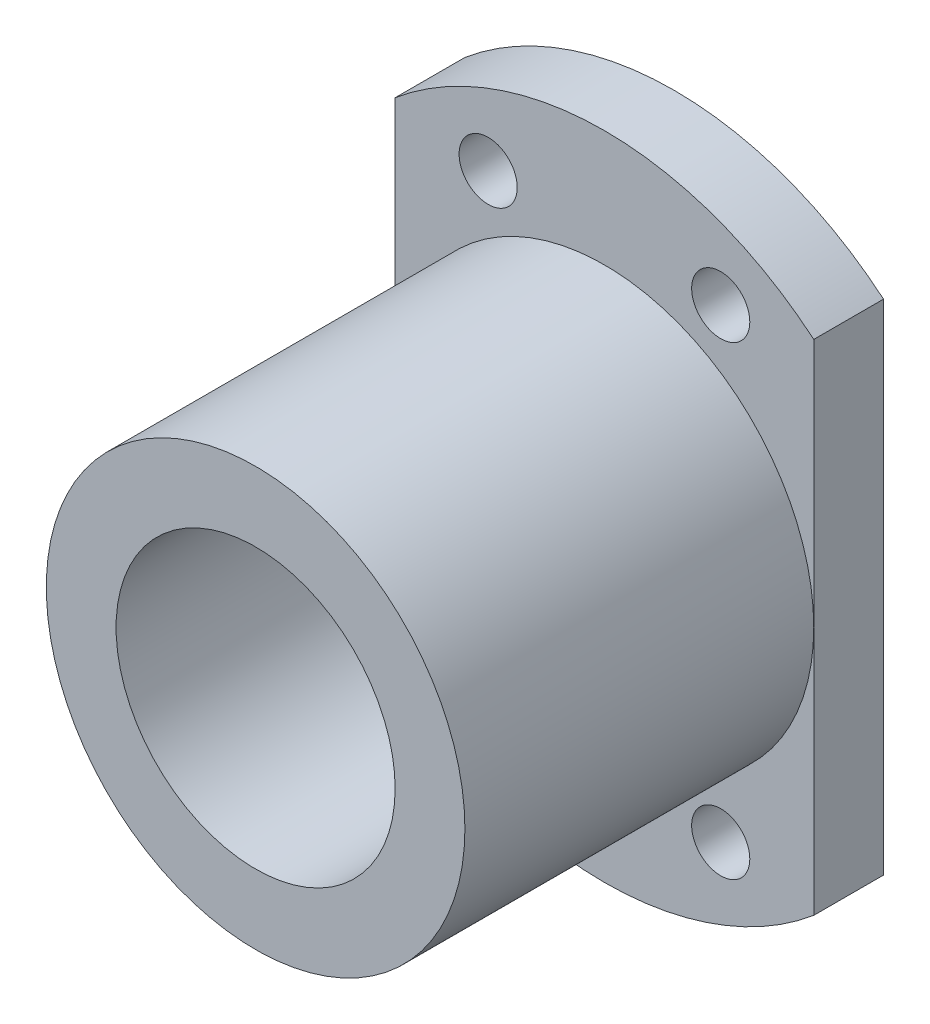
SolidWorks part; units mm, degrees
ref_plane "Front Plane" through (0, 0, 0) normal (0, 0, 1) x (1, 0, 0)
ref_plane "Top Plane" through (0, 0, 0) normal (0, 1, 0) x (1, 0, 0)
ref_plane "Right Plane" through (0, 0, 0) normal (1, 0, 0) x (0, 0, -1)
sketch "Sketch1" plane through (0, 0, 0) normal (0, 0, 1) x (1, 0, 0)
  line L0 (-9, 10.7238) -> (-9, -10.7238)
  line L1 (9, 10.7238) -> (9, -10.7238)
  line L2 (-9, 0) -> (9, 0) construction
  line L3 (-5, 10) -> (5, -10) construction
  line L4 (-5, -10) -> (5, 10) construction
  arc A0 (9, 10.7238) -> (-9, 10.7238) centre (0, 0) ccw
  arc A1 (-9, -10.7238) -> (9, -10.7238) centre (0, 0) ccw
  circle A2 centre (0, 0) radius 6
  circle A3 centre (-5, 10) radius 1.25
  circle A4 centre (5, 10) radius 1.25
  circle A5 centre (-5, -10) radius 1.25
  circle A6 centre (5, -10) radius 1.25
  point P7 (0, 0)
  point P18 (0, 0)
  dimension "D2" = 14
  dimension "D3" = 12
  dimension "D6" = 2.5
  dimension "D1" = 18
  dimension "D4" = 20
  dimension "D5" = 10
extrude "Boss-Extrude1" add sketch "Sketch1" along normal blind 3
sketch "Sketch2" plane through (0, 0, 3) normal (0, 0, 1) x (1, 0, 0)
  circle A0 centre (0, 0) radius 9
  circle A1 centre (0, 0) radius 6
  circle A2 centre (0, 0) radius 6 construction
  dimension "D1" = 18
extrude "LinearBallSupport" add sketch "Sketch2" along normal blind 15
